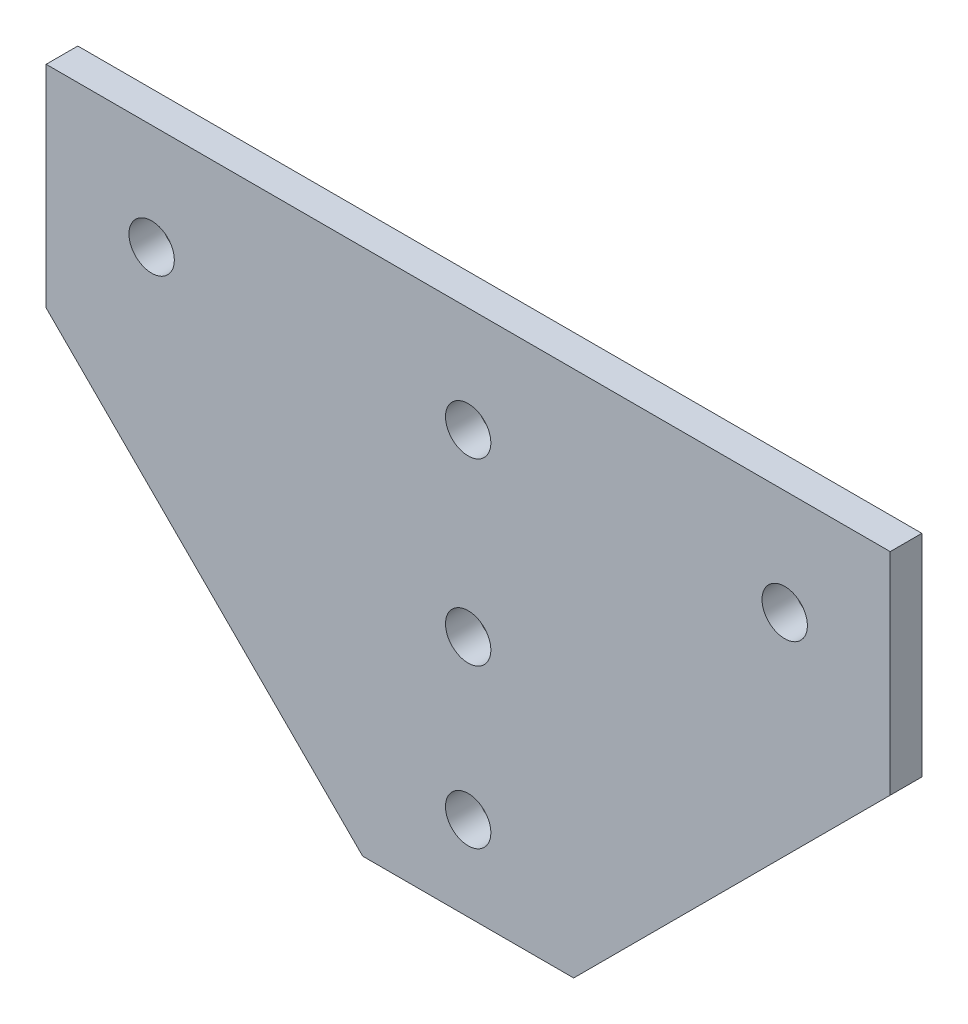
SolidWorks part; units mm, degrees
material "Thornel Mat VMA"
ref_plane "前视基准面" through (0, 0, 0) normal (0, 0, 1) x (1, 0, 0)
ref_plane "上视基准面" through (0, 0, 0) normal (0, 1, 0) x (1, 0, 0)
ref_plane "右视基准面" through (0, 0, 0) normal (1, 0, 0) x (0, 0, -1)
sketch "Sketch1" plane through (0, 0, 0) normal (0, 0, 1) x (1, 0, 0)
  line L0 (-412.095, 20) -> (-412.095, 0)
  line L1 (-472.095, 20) -> (-400.3728, 20) construction
  line L2 (-492.095, 0) -> (-382.095, 0) construction
  line L3 (-412.095, 0) -> (-382.095, -30)
  line L4 (-382.095, -180) -> (-382.095, 0) construction
  line L5 (-382.095, -30) -> (-362.095, -30)
  line L6 (-362.095, -180) -> (-362.095, 0) construction
  line L7 (-362.095, -30) -> (-332.095, 0)
  line L8 (-362.095, 0) -> (17.905, 0) construction
  line L9 (-332.095, 0) -> (-332.095, 20)
  line L10 (-492.095, 20) -> (147.905, 20) construction
  line L11 (-332.095, 20) -> (-412.095, 20)
  line L12 (-412.095, 10) -> (-332.095, 10) construction
  line L13 (-372.095, -30) -> (-372.095, 20) construction
  circle A0 centre (-402.095, 10) radius 2.15
  circle A1 centre (-342.095, 10) radius 2.15
  circle A2 centre (-372.095, -22) radius 2.15
  circle A3 centre (-372.095, -7) radius 2.15
  circle A4 centre (-372.095, 10) radius 2.15
  point P32 (-374.7733, -7.1016)
  point P33 (-372.095, 20)
  dimension "D4" = 4.3
  dimension "D5" = 10
  dimension "D6" = 10
  dimension "D7" = 8
  dimension "D8" = 15
  dimension "D1" = 30
  dimension "D2" = 30
  dimension "D3" = 30
extrude "Boss-Extrude1" add sketch "Sketch1" along normal blind 3
